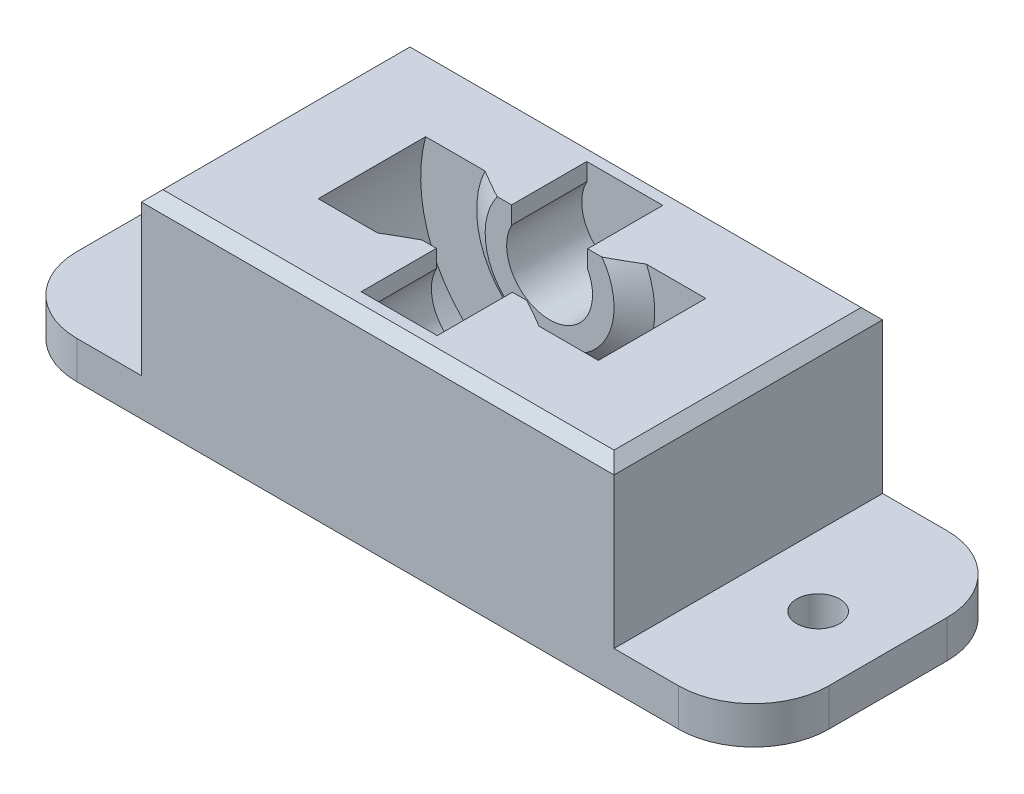
SolidWorks part; units mm, degrees
material "Nylon 101"
ref_plane "Front Plane" through (0, 0, 0) normal (0, 0, 1) x (1, 0, 0)
ref_plane "Top Plane" through (0, 0, 0) normal (0, 1, 0) x (1, 0, 0)
ref_plane "Right Plane" through (0, 0, 0) normal (1, 0, 0) x (0, 0, -1)
sketch "Sketch1" plane through (0, 0, 0) normal (0, 0, 1) x (1, 0, 0)
  line L0 (0, 38.5729) -> (0, -39.8293) construction
  line L1 (-23.0394, 7.5774) -> (-13.0394, 7.5774) construction
  line L2 (23.0394, 7.5774) -> (26, 2.5812) construction
  line L3 (26, 2.5812) -> (22, 2.5812) construction
  line L4 (22, 2.5812) -> (22, -7.4188)
  line L5 (22, -10.9188) -> (-22, -10.9188)
  line L6 (0, 15.0813) -> (38.1959, 15.0812) construction
  line L7 (-22, 2.5812) -> (-22, -7.4188)
  line L8 (-26, 2.5812) -> (-22, 2.5812) construction
  line L9 (-23.0394, 7.5774) -> (-26, 2.5812) construction
  line L10 (13.0394, 7.5774) -> (23.0394, 7.5774) construction
  line L11 (22, -7.4188) -> (35, -7.4188)
  line L12 (35, -7.4188) -> (35, -10.9188)
  line L13 (35, -10.9188) -> (22, -10.9188)
  line L14 (-22, -7.4188) -> (-35, -7.4188)
  line L15 (-35, -7.4188) -> (-35, -10.9188)
  line L16 (-35, -10.9188) -> (-22, -10.9188)
  line L17 (22, 2.5812) -> (22, 7.5774)
  line L18 (-22, 2.5812) -> (-22, 7.5774)
  line L19 (-22, 7.5774) -> (-13.0394, 7.5774)
  line L20 (13.0394, 7.5774) -> (22, 7.5774)
  arc A0 (13.0394, 7.5774) -> (-13.0394, 7.5774) centre (0, 0) ccw construction
  circle A1 centre (0, 4.0813) radius 11 construction
  arc A2 (-13.0394, 7.5774) -> (13.0394, 7.5774) centre (0, 4.0813) ccw
  point P14 (0, -10.9188)
  point P17 (0, 7.407)
  dimension "D3" = 30.1625
  dimension "D5" = 22
  dimension "D8" = 13.5
  dimension "D2" = 12.5
  dimension "D4" = 22
  dimension "D6" = 10
  dimension "D7" = 4
  dimension "D9" = 10
  dimension "D10" = 70
  dimension "D11" = 3.5
extrude "Boss-Extrude1" add sketch "Sketch1" along normal mid plane 25
ref_plane "Plane1" through (0, 0, 5) normal (0, 0, 1) x (1, 0, 0)
sketch "Sketch2" plane through (0, 0, 5) normal (0, 0, 1) x (1, 0, 0)
  line L0 (-3.5394, 5.9447) -> (-3.5394, 7.5774)
  line L1 (-3.5394, 7.5774) -> (-13.0394, 7.5774)
  line L2 (0, 4.0813) -> (0, 18.6961) construction
  line L3 (3.5394, 5.9447) -> (3.5394, 7.5774)
  line L4 (3.5394, 7.5774) -> (13.0394, 7.5774)
  arc A0 (-3.5394, 5.9447) -> (3.5394, 5.9447) centre (0, 4.0813) ccw
  arc A1 (-13.0394, 7.5774) -> (13.0394, 7.5774) centre (0, 4.0813) ccw construction
  circle A2 centre (0, 4.0813) radius 11 construction
  arc A3 (-13.0394, 7.5774) -> (13.0394, 7.5774) centre (0, 4.0813) ccw
  dimension "D1" = 22
  dimension "D2" = 4
  dimension "D3" = 9.5
extrude "Boss-Extrude2" add sketch "Sketch2" along normal up to surface (7.5 mm away) up to face at (0, -3.8199, 12.5)
ref_plane "Plane2" through (0, 0, -5) normal (0, 0, 1) x (1, 0, 0)
sketch "Sketch3" plane through (0, 0, -5) normal (0, 0, 1) x (1, 0, 0)
  line L4 (3.5394, 7.5774) -> (3.5394, 5.9447)
  line L5 (13.0394, 7.5774) -> (3.5394, 7.5774)
  line L6 (-3.5394, 7.5774) -> (-13.0394, 7.5774)
  line L7 (-3.5394, 5.9447) -> (-3.5394, 7.5774)
  line L8 (3.5394, 7.5774) -> (3.5394, 5.9447)
  line L9 (13.0394, 7.5774) -> (3.5394, 7.5774)
  line L10 (-3.5394, 7.5774) -> (-13.0394, 7.5774)
  line L11 (-3.5394, 5.9447) -> (-3.5394, 7.5774)
  arc A2 (-3.5394, 5.9447) -> (3.5394, 5.9447) centre (0, 4.0813) ccw
  arc A3 (-13.0394, 7.5774) -> (13.0394, 7.5774) centre (0, 4.0813) ccw
  arc A4 (-3.5394, 5.9447) -> (3.5394, 5.9447) centre (0, 4.0813) ccw
  arc A5 (-13.0394, 7.5774) -> (13.0394, 7.5774) centre (0, 4.0813) ccw
  dimension "D1" = 0
extrude "Boss-Extrude3" add sketch "Sketch3" against normal up to surface (7.5 mm away) up to face at (0, -3.8199, -12.5)
ref_plane "Plane3" through (0, 4.0813, 0) normal (0, 1, 0) x (1, 0, 0)
sketch "Sketch4" plane through (0, 4.0813, 0) normal (0, 1, 0) x (1, 0, 0)
  line L0 (-4, -5) -> (-4, -3.5)
  line L1 (-4, -3.5) -> (-6, -3.5)
  line L2 (-6, -3.5) -> (-8.2894, -5)
  line L3 (-3.5394, -5) -> (-13.0394, -5) construction
  line L4 (0, 0) -> (-40.6317, 0) construction
  line L5 (-4, 5) -> (-4, 3.5)
  line L6 (-4, 3.5) -> (-6, 3.5)
  line L7 (-6, 3.5) -> (-8.2894, 5)
  line L8 (-8.2894, 5) -> (-4, 5)
  line L9 (-8.2894, -5) -> (-4, -5)
  line L10 (0, 0) -> (0, 12.6772) construction
  dimension "D1" = 2
  dimension "D2" = 7
  dimension "D3" = 4
revolve "Revolve1" add sketch "Sketch4" angle 360 about L10
sketch "Sketch5" plane through (0, 7.5774, 0) normal (0, 1, 0) x (1, 0, 0)
  line L4 (35, 12.5) -> (-35, 12.5)
  line L5 (35, -12.5) -> (35, 12.5)
  line L6 (-35, -12.5) -> (35, -12.5)
  line L7 (35, -12.5) -> (35, 12.5)
  line L8 (35, 12.5) -> (-35, 12.5)
  line L9 (-35, 12.5) -> (-35, -12.5)
  line L10 (-35, -12.5) -> (35, -12.5)
  line L11 (-35, 12.5) -> (-35, -12.5)
  dimension "D1" = 0
extrude "Cut-Extrude1" cut sketch "Sketch5" along normal blind 10
sketch "Sketch6" plane through (0, 7.5774, 0) normal (0, 1, 0) x (1, 0, 0)
  line L0 (-3.5394, 5) -> (-3.5394, -5)
  line L1 (-3.5394, -5) -> (3.5394, -5)
  line L2 (3.5394, -5) -> (3.5394, 5)
  line L3 (3.5394, 5) -> (-3.5394, 5)
extrude "Cut-Extrude2" cut sketch "Sketch6" against normal up to surface (3.4962 mm away)
sketch "Sketch7" plane through (0, 0, 12.5) normal (0, 0, 1) x (1, 0, 0)
  line L0 (-22, 2.3812) -> (-22, 7.5774)
  line L2 (-22, 7.5774) -> (22, 7.5774)
  line L4 (22, 7.5774) -> (22, -3.0388)
  line L5 (22, -3.0388) -> (22, -10.9188)
  line L6 (22, -7.4188) -> (22, 7.5774) construction
  line L7 (22, -10.9188) -> (-22, -10.9188)
  line L8 (-22, 7.5774) -> (-22, -7.4188) construction
  line L9 (-22, -10.9188) -> (-22, 2.3812)
  line L10 (-3.5394, 7.5774) -> (-22, 7.5774) construction
  line L11 (-35, -10.9188) -> (35, -10.9188) construction
extrude "Boss-Extrude4" add sketch "Sketch7" against normal blind 2
mirror "Mirror1" about plane through (0, 0, 0) normal (0, 0, 1) of "Boss-Extrude4"
fillet "Fillet1" radius 7 4 edges at (-35, -9.1688, 12.5) (-35, -9.1688, -12.5) (35, -9.1688, 12.5) (35, -9.1688, -12.5)
sketch "Sketch8" plane through (0, -7.4188, 0) normal (0, 1, 0) x (1, 0, 0)
  line L0 (22, 0) -> (35, 0) construction
  line L1 (35, -5.5) -> (35, 5.5) construction
  line L2 (22, -12.5) -> (22, 12.5) construction
  line L3 (0, 0) -> (0, 20.0845) construction
  circle A0 centre (28.5, 0) radius 2
  circle A1 centre (-28.5, 0) radius 2
  dimension "D1" = 4
extrude "Cut-Extrude3" cut sketch "Sketch8" against normal blind 40
chamfer "Chamfer1" distance 1 angle 45 4 edges at (0, 7.5774, 12.5) (-22, 7.5774, 0) (0, 7.5774, -12.5) (22, 7.5774, 0)
